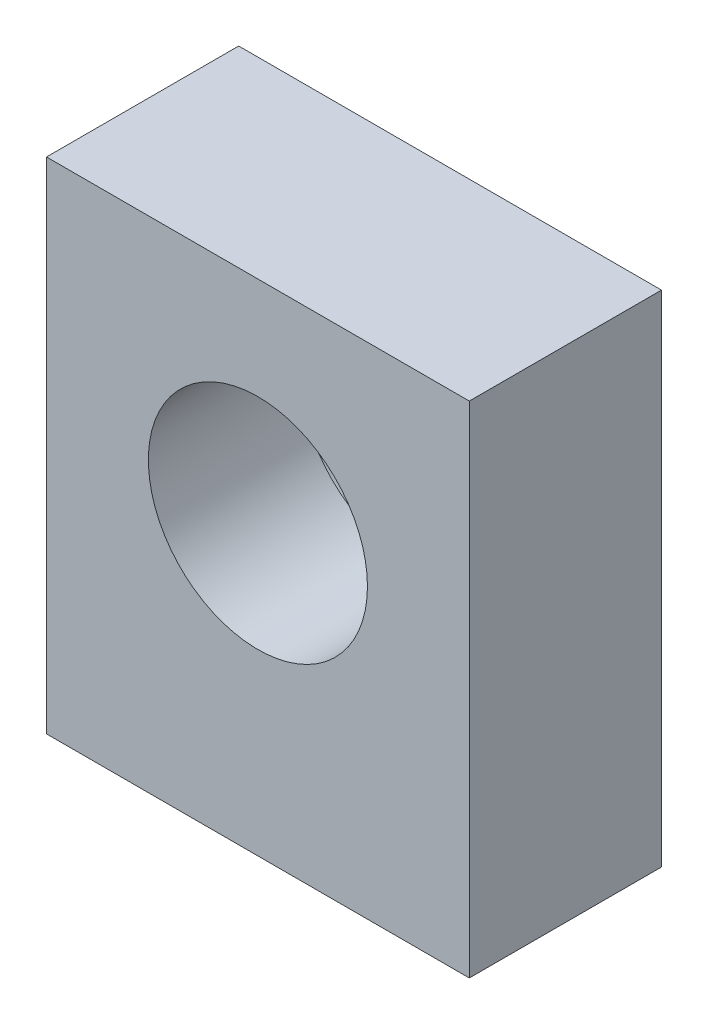
SolidWorks part; units mm, degrees
material "6061 Alloy"
ref_plane "Front Plane" through (0, 0, 0) normal (0, 0, 1) x (1, 0, 0)
ref_plane "Top Plane" through (0, 0, 0) normal (0, 1, 0) x (1, 0, 0)
ref_plane "Right Plane" through (0, 0, 0) normal (1, 0, 0) x (0, 0, -1)
sketch "Sketch1" plane through (0, 0, 0) normal (0, 1, 0) x (1, 0, 0)
  line L1 (0, 0) -> (22, 0)
  line L2 (0, 0) -> (0, 10)
  line L3 (0, 10) -> (22, 10)
  line L4 (22, 0) -> (22, 10)
  dimension "D1" = 22
  dimension "D2" = 10
extrude "Boss-Extrude1" add sketch "Sketch1" along normal blind 26
sketch "Sketch7" plane through (0, 0, 0) normal (0, 0, 1) x (1, 0, 0)
  line L3 (22, 0) -> (0, 0) construction
  line L4 (22, 26) -> (22, 0) construction
  circle A0 centre (11, 15) radius 5.7
  dimension "D1" = 11.4
  dimension "D2" = 15
  dimension "D3" = 11
extrude "Cut-Extrude1" cut sketch "Sketch7" against normal through all
sketch "Sketch9" plane through (0, 0, -10) normal (0, 0, -1) x (-1, 0, 0)
  circle A0 centre (-11, 15) radius 8.05
  dimension "D1" = 16.1
extrude "Cut-Extrude3" cut sketch "Sketch9" against normal blind 2.1
hole_wizard "M3x0.5 Tapped Hole1" positions "Sketch11" profile "Sketch10" tap size "M3x0.5" standard "ANSI Metric"
sketch "Sketch11" plane through (0, 0, 0) normal (0, -1, 0) x (-1, 0, 0)
  line L0 (0, 10) -> (0, 0) construction
  line L1 (0, 0) -> (-22, 0) construction
  line L2 (-22, 0) -> (-22, 10) construction
  line L3 (-22, 10) -> (0, 10) construction
  point P0 (-3, 3)
  point P2 (-19, 3)
  point P4 (-11, 7)
  dimension "D1" = 3
  dimension "D2" = 3
  dimension "D3" = 3
  dimension "D4" = 3
  dimension "D5" = 11
  dimension "D6" = 3
sketch "Sketch10" plane through (3, 0, -3) normal (1, 0, 0) x (0, 0, -1)
  line L0 (0, 0) -> (0, 5.7511)
  line L1 (0, 5.7511) -> (1.25, 5)
  line L2 (1.25, 5) -> (1.25, 0.275)
  line L3 (1.25, 0.275) -> (1.525, 0)
  line L5 (1.525, 0) -> (0, 0)
  line L6 (-1.25, 0.275) -> (-1.525, 0) construction
  line L10 (0, 5.7511) -> (-1.25, 5) construction
  line L11 (0, -6.35) -> (0, 107.95) construction
  dimension "Tap Drill Dia." = 2.5
  dimension "Tap Drill Depth" = 5
  dimension "Near C'Sink Dia." = 3.05
  dimension "Near C'Sink Angle" = 90
  dimension "Drill Angle" = 118
cosmetic thread "Hole Thread6" parameters "D1"=5, "D2"=3
cosmetic thread "Hole Thread7" parameters "D1"=5, "D2"=3
cosmetic thread "Hole Thread8" parameters "D1"=5, "D2"=3
